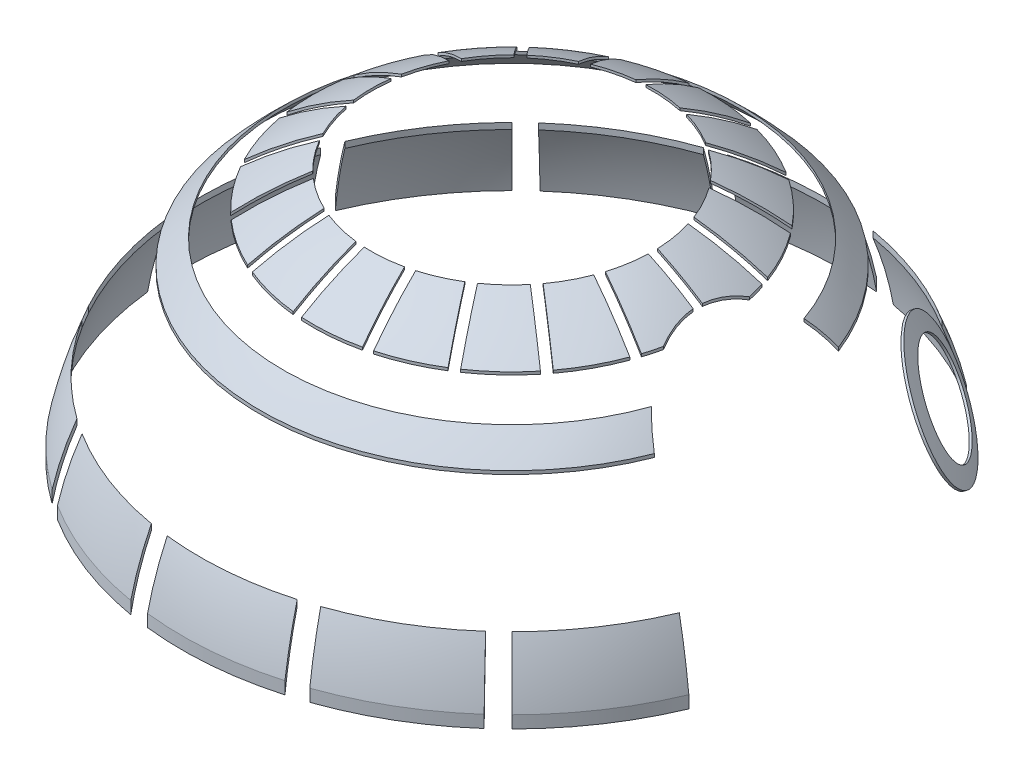
SolidWorks part; units mm, degrees
ref_plane "前视基准面" through (0, 0, 0) normal (0, 0, 1) x (1, 0, 0)
ref_plane "上视基准面" through (0, 0, 0) normal (0, 1, 0) x (1, 0, 0)
ref_plane "右视基准面" through (0, 0, 0) normal (1, 0, 0) x (0, 0, -1)
sketch "草图1" plane through (0, 0, 0) normal (0, 0, 1) x (1, 0, 0)
  line L0 (0, 0) -> (0, 255.8429) construction
  line L1 (-75, 129.2321) -> (0, 129.2321)
  line L2 (0, 129.2321) -> (0, 204.2321)
  arc A0 (-75, 129.2321) -> (0, 204.2321) centre (0, 129.2321) cw
revolve "旋转1" add sketch "草图1" angle 360 about L0
shell "抽壳1" thickness 0.5
sketch "草图2" plane through (0, 0, 0) normal (0, 1, 0) x (1, 0, 0)
  line L0 (64.568, -27.0365) -> (68.2576, -28.5815)
  line L1 (49.4975, -49.4975) -> (52.3259, -52.3259)
  line L2 (23.5611, -37.9404) -> (16.4337, -27.0311)
  line L3 (8.7572, -30.3983) -> (11.9562, -43.0308)
  line L4 (23.5611, -37.9404) -> (16.4337, -27.0311)
  line L5 (8.7572, -30.3983) -> (11.9562, -43.0308)
  line L6 (34.6037, -28.2344) -> (24.3202, -20.2305)
  line L7 (18.153, -25.9078) -> (25.2804, -36.8171)
  line L8 (34.6037, -28.2344) -> (24.3202, -20.2305)
  line L9 (18.153, -25.9078) -> (25.2804, -36.8171)
  line L10 (25.5817, -18.6098) -> (35.8651, -26.6137)
  line L11 (41.8965, -15.4688) -> (29.5713, -11.2375)
  line L12 (25.5817, -18.6098) -> (35.8651, -26.6137)
  line L13 (41.8965, -15.4688) -> (29.5713, -11.2375)
  line L14 (-30.9955, -32.1539) -> (-22.1697, -22.5665)
  line L15 (-27.3184, -15.9516) -> (-38.779, -22.1537)
  line L16 (-30.9955, -32.1539) -> (-22.1697, -22.5665)
  line L17 (-27.3184, -15.9516) -> (-38.779, -22.1537)
  line L18 (-18.8757, -40.476) -> (-13.6411, -28.5423)
  line L19 (-20.6587, -23.9575) -> (-29.4845, -33.5449)
  line L20 (-18.8757, -40.476) -> (-13.6411, -28.5423)
  line L21 (-20.6587, -23.9575) -> (-29.4845, -33.5449)
  line L22 (9.9653, -43.5349) -> (6.7663, -30.9025)
  line L23 (-1.5876, -31.5947) -> (-2.6637, -44.5814)
  line L24 (9.9653, -43.5349) -> (6.7663, -30.9025)
  line L25 (-1.5876, -31.5947) -> (-2.6637, -44.5814)
  line L26 (-11.7604, -29.3673) -> (-16.995, -41.301)
  line L27 (-4.7105, -44.4118) -> (-3.6344, -31.4251)
  line L28 (-11.7604, -29.3673) -> (-16.995, -41.301)
  line L29 (-4.7105, -44.4118) -> (-3.6344, -31.4251)
  line L30 (-38.779, 22.1537) -> (-27.3184, 15.9516)
  line L31 (-22.1697, 22.5665) -> (-30.9955, 32.1539)
  line L32 (-38.779, 22.1537) -> (-27.3184, 15.9516)
  line L33 (-22.1697, 22.5665) -> (-30.9955, 32.1539)
  line L34 (-43.8711, 8.3619) -> (-31.0176, 6.217)
  line L35 (-28.2958, 14.1453) -> (-39.7565, 20.3475)
  line L36 (-43.8711, 8.3619) -> (-31.0176, 6.217)
  line L37 (-28.2958, 14.1453) -> (-39.7565, 20.3475)
  line L38 (-39.7565, -20.3475) -> (-28.2958, -14.1453)
  line L39 (-31.0176, -6.217) -> (-43.8711, -8.3619)
  line L40 (-39.7565, -20.3475) -> (-28.2958, -14.1453)
  line L41 (-31.0176, -6.217) -> (-43.8711, -8.3619)
  line L42 (-31.3557, 4.1913) -> (-44.2092, 6.3361)
  line L43 (-44.2092, -6.3361) -> (-31.3557, -4.1913)
  line L44 (-31.3557, 4.1913) -> (-44.2092, 6.3361)
  line L45 (-44.2092, -6.3361) -> (-31.3557, -4.1913)
  line L46 (11.9562, 43.0308) -> (8.7572, 30.3983)
  line L47 (16.4337, 27.0311) -> (23.5611, 37.9404)
  line L48 (11.9562, 43.0308) -> (8.7572, 30.3983)
  line L49 (16.4337, 27.0311) -> (23.5611, 37.9404)
  line L50 (-2.6637, 44.5814) -> (-1.5876, 31.5947)
  line L51 (6.7663, 30.9025) -> (9.9653, 43.5349)
  line L52 (-2.6637, 44.5814) -> (-1.5876, 31.5947)
  line L53 (6.7663, 30.9025) -> (9.9653, 43.5349)
  line L54 (-29.4845, 33.5449) -> (-20.6587, 23.9575)
  line L55 (-13.6411, 28.5423) -> (-18.8757, 40.476)
  line L56 (-29.4845, 33.5449) -> (-20.6587, 23.9575)
  line L57 (-13.6411, 28.5423) -> (-18.8757, 40.476)
  line L58 (-3.6344, 31.4251) -> (-4.7105, 44.4118)
  line L59 (-16.995, 41.301) -> (-11.7604, 29.3673)
  line L60 (-3.6344, 31.4251) -> (-4.7105, 44.4118)
  line L61 (-16.995, 41.301) -> (-11.7604, 29.3673)
  line L62 (25.2804, 36.8171) -> (18.153, 25.9078)
  line L63 (24.3202, 20.2305) -> (34.6037, 28.2344)
  line L64 (25.2804, 36.8171) -> (18.153, 25.9078)
  line L65 (24.3202, 20.2305) -> (34.6037, 28.2344)
  line L66 (29.5713, 11.2375) -> (41.8965, 15.4688)
  line L67 (35.8651, 26.6137) -> (25.5817, 18.6098)
  line L68 (29.5713, 11.2375) -> (41.8965, 15.4688)
  line L69 (35.8651, 26.6137) -> (25.5817, 18.6098)
  line L70 (30.2382, -9.2951) -> (42.5633, -13.5263)
  line L71 (41.6885, -1.0269) -> (31.6179, -1.0269)
  line L72 (30.2382, -9.2951) -> (42.5633, -13.5263)
  line L73 (41.6885, -1.0269) -> (31.6179, -1.0269)
  line L74 (31.6179, 1.0269) -> (41.6885, 1.0269)
  line L75 (42.5633, 13.5263) -> (30.2382, 9.2951)
  line L76 (31.6179, 1.0269) -> (41.6885, 1.0269)
  line L77 (42.5633, 13.5263) -> (30.2382, 9.2951)
  line L78 (46.443, -52.3741) -> (49.0969, -55.3669)
  line L79 (23.1195, -66.0718) -> (24.4407, -69.8474)
  line L80 (19.1195, -67.3383) -> (20.212, -71.1862)
  line L81 (-7.8375, -69.5599) -> (-8.2854, -73.5347)
  line L82 (-11.991, -68.9653) -> (-12.6762, -72.9062)
  line L83 (-37.2422, -59.2707) -> (-39.3704, -62.6576)
  line L84 (-40.7264, -56.9329) -> (-43.0536, -60.1862)
  line L85 (-59.2707, -37.2422) -> (-62.6576, -39.3704)
  line L86 (-61.3955, -33.6243) -> (-64.9038, -35.5457)
  line L87 (-69.5599, -7.8375) -> (-73.5347, -8.2854)
  line L88 (-69.9045, -3.6559) -> (-73.899, -3.8648)
  line L89 (-66.0718, 23.1195) -> (-69.8474, 24.4407)
  line L90 (-64.568, 27.0365) -> (-68.2576, 28.5815)
  line L91 (-49.4975, 49.4975) -> (-52.3259, 52.3259)
  line L92 (-46.443, 52.3741) -> (-49.0969, 55.3669)
  line L93 (-23.1195, 66.0718) -> (-24.4407, 69.8474)
  line L94 (-19.1195, 67.3383) -> (-20.212, 71.1862)
  line L95 (7.8375, 69.5599) -> (8.2854, 73.5347)
  line L96 (11.991, 68.9653) -> (12.6762, 72.9062)
  line L97 (37.2422, 59.2707) -> (39.3704, 62.6576)
  line L98 (36.3071, 53.036) -> (53.5447, 70.2737)
  line L99 (53.5447, 70.2737) -> (77.689, 36.8171)
  line L100 (77.689, 36.8171) -> (59.1806, 26.6137)
  line L101 (59.1806, 26.6137) -> (36.3071, 53.036)
  line L104 (69.9045, 3.6559) -> (73.899, 3.8648) [skipped]
  line L105 (66.0718, -23.1195) -> (69.8474, -24.4407) [skipped]
  line L106 (69.5599, 7.8375) -> (73.5347, 8.2854) [skipped]
  line L107 (61.3955, 33.6243) -> (64.9038, 35.5457) [skipped]
  line L108 (59.2707, 37.2422) -> (62.6576, 39.3704) [skipped]
  line L109 (40.7264, 56.9329) -> (43.0536, 60.1862) [skipped]
  arc A0 (49.4975, -49.4975) -> (64.568, -27.0365) centre (0, 0) ccw
  arc A1 (52.3259, -52.3259) -> (68.2576, -28.5815) centre (0, 0) ccw
  arc A2 (8.7572, -30.3983) -> (16.4337, -27.0311) centre (0, 0) ccw
  arc A3 (11.9562, -43.0308) -> (23.5611, -37.9404) centre (0, 0) ccw
  arc A4 (48.4285, 17.1076) -> (48.4285, -17.1076) centre (0, 0) ccw
  arc A5 (48.4285, -17.1076) -> (52.6029, -20.6814) centre (66.6919, 0) ccw
  arc A6 (52.6029, 20.6814) -> (52.6029, -20.6814) centre (0, 0) ccw
  arc A7 (52.6029, 20.6814) -> (48.4285, 17.1076) centre (66.6919, 0) ccw
  arc A8 (48.4285, 17.1076) -> (48.4285, -17.1076) centre (0, 0) ccw
  arc A9 (48.4285, -17.1076) -> (52.6029, -20.6814) centre (66.6919, 0) ccw
  arc A10 (52.6029, 20.6814) -> (52.6029, -20.6814) centre (0, 0) ccw
  arc A11 (52.6029, 20.6814) -> (48.4285, 17.1076) centre (66.6919, 0) ccw
  arc A12 (8.7572, -30.3983) -> (16.4337, -27.0311) centre (0, 0) ccw
  arc A13 (11.9562, -43.0308) -> (23.5611, -37.9404) centre (0, 0) ccw
  arc A14 (18.153, -25.9078) -> (24.3202, -20.2305) centre (0, 0) ccw
  arc A15 (25.2804, -36.8171) -> (34.6037, -28.2344) centre (0, 0) ccw
  arc A16 (18.153, -25.9078) -> (24.3202, -20.2305) centre (0, 0) ccw
  arc A17 (25.2804, -36.8171) -> (34.6037, -28.2344) centre (0, 0) ccw
  arc A18 (25.5817, -18.6098) -> (29.5713, -11.2375) centre (0, 0) ccw
  arc A19 (35.8651, -26.6137) -> (41.8965, -15.4688) centre (0, 0) ccw
  arc A20 (25.5817, -18.6098) -> (29.5713, -11.2375) centre (0, 0) ccw
  arc A21 (35.8651, -26.6137) -> (41.8965, -15.4688) centre (0, 0) ccw
  arc A22 (-27.3184, -15.9516) -> (-22.1697, -22.5665) centre (0, 0) ccw
  arc A23 (-38.779, -22.1537) -> (-30.9955, -32.1539) centre (0, 0) ccw
  arc A24 (-27.3184, -15.9516) -> (-22.1697, -22.5665) centre (0, 0) ccw
  arc A25 (-38.779, -22.1537) -> (-30.9955, -32.1539) centre (0, 0) ccw
  arc A26 (-20.6587, -23.9575) -> (-13.6411, -28.5423) centre (0, 0) ccw
  arc A27 (-29.4845, -33.5449) -> (-18.8757, -40.476) centre (0, 0) ccw
  arc A28 (-20.6587, -23.9575) -> (-13.6411, -28.5423) centre (0, 0) ccw
  arc A29 (-29.4845, -33.5449) -> (-18.8757, -40.476) centre (0, 0) ccw
  arc A30 (-1.5876, -31.5947) -> (6.7663, -30.9025) centre (0, 0) ccw
  arc A31 (-2.6637, -44.5814) -> (9.9653, -43.5349) centre (0, 0) ccw
  arc A32 (-1.5876, -31.5947) -> (6.7663, -30.9025) centre (0, 0) ccw
  arc A33 (-2.6637, -44.5814) -> (9.9653, -43.5349) centre (0, 0) ccw
  arc A34 (-11.7604, -29.3673) -> (-3.6344, -31.4251) centre (0, 0) ccw
  arc A35 (-16.995, -41.301) -> (-4.7105, -44.4118) centre (0, 0) ccw
  arc A36 (-11.7604, -29.3673) -> (-3.6344, -31.4251) centre (0, 0) ccw
  arc A37 (-16.995, -41.301) -> (-4.7105, -44.4118) centre (0, 0) ccw
  arc A38 (-22.1697, 22.5665) -> (-27.3184, 15.9516) centre (0, 0) ccw
  arc A39 (-30.9955, 32.1539) -> (-38.779, 22.1537) centre (0, 0) ccw
  arc A40 (-22.1697, 22.5665) -> (-27.3184, 15.9516) centre (0, 0) ccw
  arc A41 (-30.9955, 32.1539) -> (-38.779, 22.1537) centre (0, 0) ccw
  arc A42 (-28.2958, 14.1453) -> (-31.0176, 6.217) centre (0, 0) ccw
  arc A43 (-39.7565, 20.3475) -> (-43.8711, 8.3619) centre (0, 0) ccw
  arc A44 (-28.2958, 14.1453) -> (-31.0176, 6.217) centre (0, 0) ccw
  arc A45 (-39.7565, 20.3475) -> (-43.8711, 8.3619) centre (0, 0) ccw
  arc A46 (-31.0176, -6.217) -> (-28.2958, -14.1453) centre (0, 0) ccw
  arc A47 (-43.8711, -8.3619) -> (-39.7565, -20.3475) centre (0, 0) ccw
  arc A48 (-31.0176, -6.217) -> (-28.2958, -14.1453) centre (0, 0) ccw
  arc A49 (-43.8711, -8.3619) -> (-39.7565, -20.3475) centre (0, 0) ccw
  arc A50 (-31.3557, 4.1913) -> (-31.3557, -4.1913) centre (0, 0) ccw
  arc A51 (-44.2092, 6.3361) -> (-44.2092, -6.3361) centre (0, 0) ccw
  arc A52 (-31.3557, 4.1913) -> (-31.3557, -4.1913) centre (0, 0) ccw
  arc A53 (-44.2092, 6.3361) -> (-44.2092, -6.3361) centre (0, 0) ccw
  arc A54 (16.4337, 27.0311) -> (8.7572, 30.3983) centre (0, 0) ccw
  arc A55 (23.5611, 37.9404) -> (11.9562, 43.0308) centre (0, 0) ccw
  arc A56 (16.4337, 27.0311) -> (8.7572, 30.3983) centre (0, 0) ccw
  arc A57 (23.5611, 37.9404) -> (11.9562, 43.0308) centre (0, 0) ccw
  arc A58 (6.7663, 30.9025) -> (-1.5876, 31.5947) centre (0, 0) ccw
  arc A59 (9.9653, 43.5349) -> (-2.6637, 44.5814) centre (0, 0) ccw
  arc A60 (6.7663, 30.9025) -> (-1.5876, 31.5947) centre (0, 0) ccw
  arc A61 (9.9653, 43.5349) -> (-2.6637, 44.5814) centre (0, 0) ccw
  arc A62 (-13.6411, 28.5423) -> (-20.6587, 23.9575) centre (0, 0) ccw
  arc A63 (-18.8757, 40.476) -> (-29.4845, 33.5449) centre (0, 0) ccw
  arc A64 (-13.6411, 28.5423) -> (-20.6587, 23.9575) centre (0, 0) ccw
  arc A65 (-18.8757, 40.476) -> (-29.4845, 33.5449) centre (0, 0) ccw
  arc A66 (-3.6344, 31.4251) -> (-11.7604, 29.3673) centre (0, 0) ccw
  arc A67 (-4.7105, 44.4118) -> (-16.995, 41.301) centre (0, 0) ccw
  arc A68 (-3.6344, 31.4251) -> (-11.7604, 29.3673) centre (0, 0) ccw
  arc A69 (-4.7105, 44.4118) -> (-16.995, 41.301) centre (0, 0) ccw
  arc A70 (24.3202, 20.2305) -> (18.153, 25.9078) centre (0, 0) ccw
  arc A71 (34.6037, 28.2344) -> (25.2804, 36.8171) centre (0, 0) ccw
  arc A72 (24.3202, 20.2305) -> (18.153, 25.9078) centre (0, 0) ccw
  arc A73 (34.6037, 28.2344) -> (25.2804, 36.8171) centre (0, 0) ccw
  arc A74 (29.5713, 11.2375) -> (25.5817, 18.6098) centre (0, 0) ccw
  arc A75 (41.8965, 15.4688) -> (35.8651, 26.6137) centre (0, 0) ccw
  arc A76 (29.5713, 11.2375) -> (25.5817, 18.6098) centre (0, 0) ccw
  arc A77 (41.8965, 15.4688) -> (35.8651, 26.6137) centre (0, 0) ccw
  arc A78 (23.1195, -66.0718) -> (46.443, -52.3741) centre (0, 0) ccw
  arc A79 (41.6885, -1.0269) -> (43.6049, -9.6546) centre (66.6919, 0) ccw
  arc A80 (42.5633, -13.5263) -> (43.6049, -9.6546) centre (0, 0) ccw
  arc A81 (30.2382, -9.2951) -> (31.6179, -1.0269) centre (0, 0) ccw
  arc A82 (41.6885, -1.0269) -> (43.6049, -9.6546) centre (66.6919, 0) ccw
  arc A83 (42.5633, -13.5263) -> (43.6049, -9.6546) centre (0, 0) ccw
  arc A84 (30.2382, -9.2951) -> (31.6179, -1.0269) centre (0, 0) ccw
  arc A85 (31.6179, 1.0269) -> (30.2382, 9.2951) centre (0, 0) ccw
  arc A86 (43.6049, 9.6546) -> (42.5633, 13.5263) centre (0, 0) ccw
  arc A87 (43.6049, 9.6546) -> (41.6885, 1.0269) centre (66.6919, 0) ccw
  arc A88 (31.6179, 1.0269) -> (30.2382, 9.2951) centre (0, 0) ccw
  arc A89 (43.6049, 9.6546) -> (42.5633, 13.5263) centre (0, 0) ccw
  arc A90 (43.6049, 9.6546) -> (41.6885, 1.0269) centre (66.6919, 0) ccw
  arc A91 (24.4407, -69.8474) -> (49.0969, -55.3669) centre (0, 0) ccw
  arc A92 (-7.8375, -69.5599) -> (19.1195, -67.3383) centre (0, 0) ccw
  arc A93 (-8.2854, -73.5347) -> (20.212, -71.1862) centre (0, 0) ccw
  arc A94 (-37.2422, -59.2707) -> (-11.991, -68.9653) centre (0, 0) ccw
  arc A95 (-39.3704, -62.6576) -> (-12.6762, -72.9062) centre (0, 0) ccw
  arc A96 (-59.2707, -37.2422) -> (-40.7264, -56.9329) centre (0, 0) ccw
  arc A97 (-62.6576, -39.3704) -> (-43.0536, -60.1862) centre (0, 0) ccw
  arc A98 (-69.5599, -7.8375) -> (-61.3955, -33.6243) centre (0, 0) ccw
  arc A99 (-73.5347, -8.2854) -> (-64.9038, -35.5457) centre (0, 0) ccw
  arc A100 (-66.0718, 23.1195) -> (-69.9045, -3.6559) centre (0, 0) ccw
  arc A101 (-69.8474, 24.4407) -> (-73.899, -3.8648) centre (0, 0) ccw
  arc A102 (-49.4975, 49.4975) -> (-64.568, 27.0365) centre (0, 0) ccw
  arc A103 (-52.3259, 52.3259) -> (-68.2576, 28.5815) centre (0, 0) ccw
  arc A104 (-23.1195, 66.0718) -> (-46.443, 52.3741) centre (0, 0) ccw
  arc A105 (-24.4407, 69.8474) -> (-49.0969, 55.3669) centre (0, 0) ccw
  arc A106 (7.8375, 69.5599) -> (-19.1195, 67.3383) centre (0, 0) ccw
  arc A107 (8.2854, 73.5347) -> (-20.212, 71.1862) centre (0, 0) ccw
  arc A108 (37.2422, 59.2707) -> (11.991, 68.9653) centre (0, 0) ccw
  arc A109 (39.3704, 62.6576) -> (12.6762, 72.9062) centre (0, 0) ccw
  arc A116 (69.8474, -24.4407) -> (73.899, 3.8648) centre (0, 0) ccw [skipped]
  arc A117 (66.0718, -23.1195) -> (69.9045, 3.6559) centre (0, 0) ccw [skipped]
  arc A118 (69.5599, 7.8375) -> (61.3955, 33.6243) centre (0, 0) ccw [skipped]
  arc A119 (73.5347, 8.2854) -> (64.9038, 35.5457) centre (0, 0) ccw [skipped]
  arc A120 (62.6576, 39.3704) -> (43.0536, 60.1862) centre (0, 0) ccw [skipped]
  arc A121 (59.2707, 37.2422) -> (40.7264, 56.9329) centre (0, 0) ccw [skipped]
  point P185 (0, 0)
  dimension "D21" = 14
  dimension "D22" = 74
  dimension "D23" = 70
  dimension "D1" = 0
  dimension "D2" = 0
  dimension "D3" = 0
  dimension "D4" = 0
  dimension "D5" = 0
  dimension "D6" = 0
  dimension "D7" = 0
  dimension "D8" = 0
  dimension "D9" = 0
  dimension "D10" = 0
  dimension "D11" = 0
  dimension "D12" = 0
  dimension "D13" = 0
  dimension "D14" = 0
  dimension "D15" = 0
  dimension "D16" = 0
  dimension "D17" = 0
  dimension "D18" = 0
  dimension "D19" = 0
  dimension "D20" = 0
extrude "切除-拉伸1" cut sketch "草图2" along normal blind 255 flip side to cut
sketch "草图4" plane through (92.0496, 49.6438, -76.5058) normal (-0.7104, -0.3831, 0.5904) x (0.5502, 0.2209, 0.8053)
  line L0 (0.4417, 89.8508) -> (13.49, 138.2412)
  line L1 (13.49, 138.2412) -> (50.9416, 126.3754)
  line L2 (50.9416, 126.3754) -> (39.8174, 72.2374)
  line L3 (39.8174, 72.2374) -> (0.4417, 89.8508)
  circle A0 centre (28.5442, 115.9087) radius 11
  circle A1 centre (28.5442, 115.9087) radius 15
  dimension "D1" = 22
  dimension "D2" = 30
extrude "切除-拉伸2" cut sketch "草图4" along normal blind 20 contours L3 L2 L1 L0 A1 | A0
